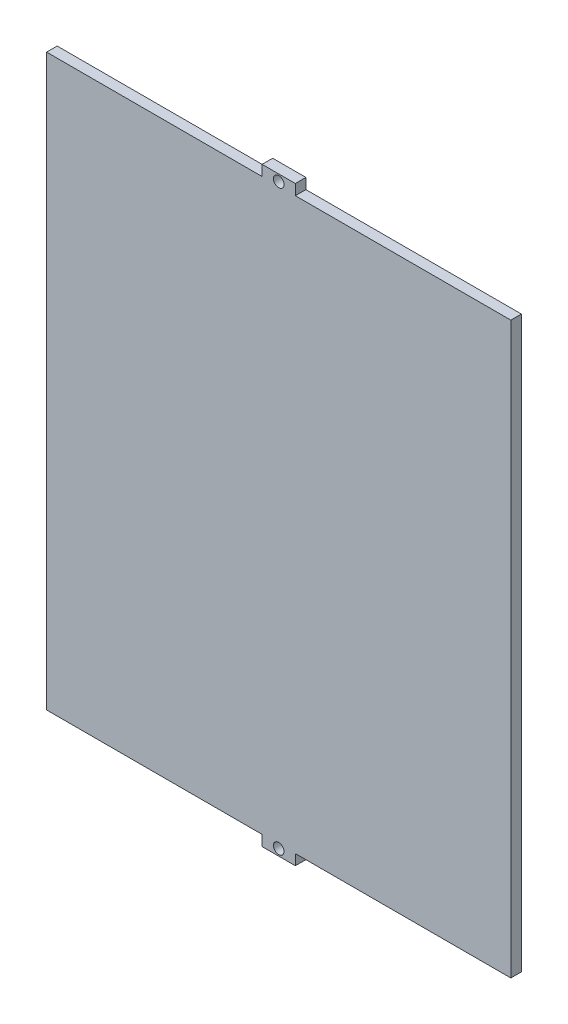
SolidWorks part; units mm, degrees
ref_plane "Front Plane" through (0, 0, 0) normal (0, 0, 1) x (1, 0, 0)
ref_plane "Top Plane" through (0, 0, 0) normal (0, 1, 0) x (1, 0, 0)
ref_plane "Right Plane" through (0, 0, 0) normal (1, 0, 0) x (0, 0, -1)
sketch "Sketch1" plane through (0, 0, 0) normal (0, 0, 1) x (1, 0, 0)
  line L1 (-69.85, 88.9) -> (69.85, 88.9)
  line L2 (-69.85, 88.9) -> (-69.85, -88.9)
  line L3 (-69.85, -88.9) -> (69.85, -88.9)
  line L4 (69.85, 88.9) -> (69.85, -88.9)
  line L5 (-69.85, 88.9) -> (69.85, -88.9) construction
  line L6 (-69.85, -88.9) -> (69.85, 88.9) construction
  point P0 (0, 0)
  dimension "D1" = 139.7
  dimension "D2" = 177.8
extrude "Boss-Extrude1" add sketch "Sketch1" along normal blind 3.18
sketch "Sketch3" plane through (0, 0, 3.18) normal (0, 0, 1) x (1, 0, 0)
  line L0 (-69.85, -88.9) -> (69.85, -88.9) construction
  line L1 (-69.85, -88.9) -> (-5, -88.9)
  line L2 (-69.85, -88.9) -> (-69.85, -85.72)
  line L3 (-69.85, -85.72) -> (-5, -85.72)
  line L4 (-5, -88.9) -> (-5, -85.72)
  line L9 (0, -88.9) -> (0, -70.9383) construction
  line L10 (5, -88.9) -> (5, -85.72)
  line L11 (69.85, -85.72) -> (5, -85.72)
  line L12 (69.85, -88.9) -> (69.85, -85.72)
  line L13 (69.85, -88.9) -> (5, -88.9)
  line L14 (69.85, 0) -> (-69.85, 0) construction
  line L15 (69.85, -88.9) -> (69.85, 88.9) construction
  line L16 (-69.85, 88.9) -> (-69.85, -88.9) construction
  line L17 (-69.85, 85.72) -> (-5, 85.72)
  line L18 (-69.85, 88.9) -> (-69.85, 85.72)
  line L19 (-69.85, 88.9) -> (-5, 88.9)
  line L20 (0, 88.9) -> (0, 70.9383) construction
  line L21 (69.85, 88.9) -> (5, 88.9)
  line L22 (69.85, 88.9) -> (69.85, 85.72)
  line L23 (69.85, 85.72) -> (5, 85.72)
  line L24 (5, 88.9) -> (5, 85.72)
  line L25 (-5, 88.9) -> (-5, 85.72)
  circle A0 centre (0, -86.9) radius 1.59
  circle A1 centre (0, 86.9) radius 1.59
  dimension "D5" = 3.18
  dimension "D6" = 2
  dimension "D1" = 3.18
  dimension "D2" = 5
extrude "Cut-Extrude2" cut sketch "Sketch3" against normal blind 10
